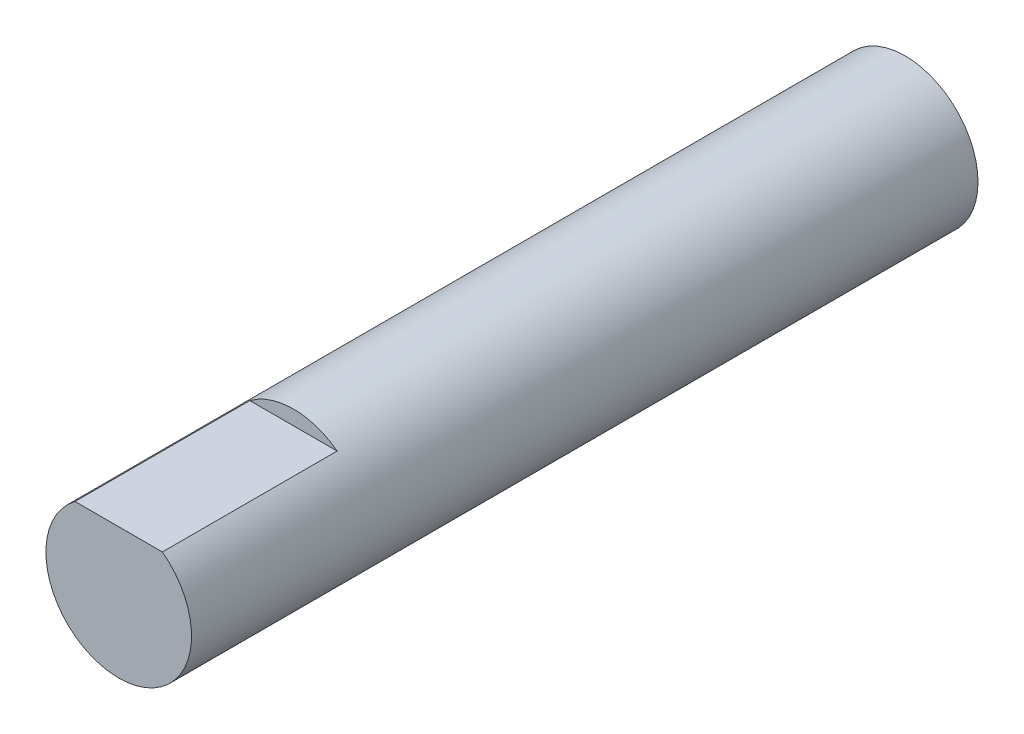
SolidWorks part; units mm, degrees
ref_plane "Front Plane" through (0, 0, 0) normal (0, 0, 1) x (1, 0, 0)
ref_plane "Top Plane" through (0, 0, 0) normal (0, 1, 0) x (1, 0, 0)
ref_plane "Right Plane" through (0, 0, 0) normal (1, 0, 0) x (0, 0, -1)
sketch "Sketch1" plane through (0, 0, 0) normal (0, 0, 1) x (1, 0, 0)
  circle A0 centre (0, 0) radius 2.5
  dimension "D1" = 5
extrude "Boss-Extrude1" add sketch "Sketch1" along normal blind 27
sketch "Sketch2" plane through (0, 0, 27) normal (0, 0, 1) x (1, 0, 0)
  line L0 (-1.5, 2) -> (1.5, 2)
  circle A1 centre (0, 0) radius 2.5
  circle A2 centre (0, 0) radius 2.5
  point P0 (0, 2.5)
  circle M3 centre (0, 0) radius 2.5
  dimension "D2" = 0.5
  dimension "D1" = 0
extrude "Cut-Extrude1" cut sketch "Sketch2" against normal blind 6 contours L0 M3
